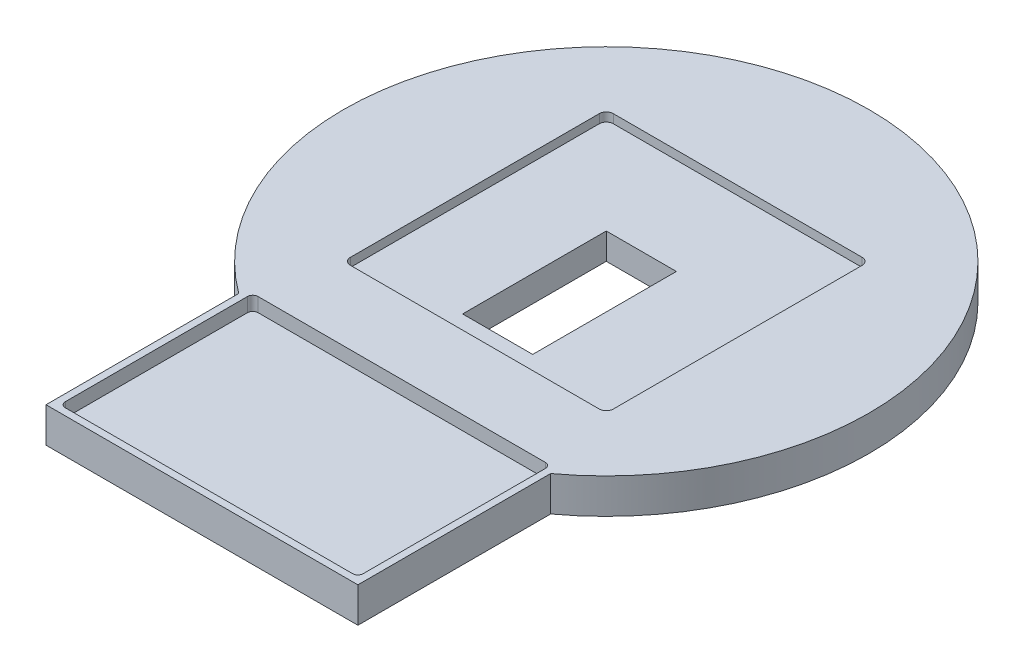
SolidWorks part; units mm, degrees
ref_plane "Front Plane" through (0, 0, 0) normal (0, 0, 1) x (1, 0, 0)
ref_plane "Top Plane" through (0, 0, 0) normal (0, 1, 0) x (1, 0, 0)
ref_plane "Right Plane" through (0, 0, 0) normal (1, 0, 0) x (0, 0, -1)
sketch "Sketch2" plane through (0, 0, 0) normal (0, 1, 0) x (1, 0, 0)
  line L0 (0, 0) -> (-44.5, 0) construction
  line L1 (-44.5, 0) -> (-44.5, -60.3718) construction
  line L2 (-44.5, -60.3718) -> (-44.5, -115.3718)
  line L3 (-44.5, -60.3718) -> (44.5, -60.3718) construction
  line L4 (-44.5, -115.3718) -> (44.5, -115.3718)
  line L5 (44.5, -115.3718) -> (44.5, -60.3718)
  arc A0 (44.5, -60.3718) -> (-44.5, -60.3718) centre (0, 0) ccw
  dimension "D1" = 150
  dimension "D2" = 44.5
  dimension "D3" = 55
extrude "Boss-Extrude2" add sketch "Sketch2" along normal blind 10
sketch "Sketch3" plane through (0, 0, 0) normal (0, 1, 0) x (1, 0, 0)
  line L0 (0, 0) -> (37.5, 0) construction
  line L1 (0, 0) -> (0, 37.5) construction
  line L2 (-37.5, 37.5) -> (37.5, 37.5)
  line L3 (37.5, 37.5) -> (37.5, -37.5)
  line L4 (-37.5, 37.5) -> (-37.5, -37.5)
  line L5 (-37.5, -37.5) -> (37.5, -37.5)
  point P6 (0, 0)
  point P9 (-37.5, 0)
  dimension "D1" = 37.5
extrude "Cut-Extrude2" cut sketch "Sketch3" against normal blind 2.5 from offset 10
fillet "Fillet2" radius 2 4 edges at (37.5, 8.75, 37.5) (-37.5, 8.75, 37.5) (-37.5, 8.75, -37.5) (37.5, 8.75, -37.5)
sketch "Sketch5" plane through (0, 0, 0) normal (0, 1, 0) x (1, 0, 0)
  line L0 (-44.5, -113.3718) -> (-42.5, -113.3718) construction
  line L1 (-44.5, -60.3718) -> (-44.5, -115.3718) construction
  line L2 (-42.5, -113.3718) -> (-42.5, -115.3718) construction
  line L3 (-44.5, -115.3718) -> (44.5, -115.3718) construction
  line L4 (-42.5, -113.3718) -> (-42.5, -58.3718)
  line L5 (-42.5, -58.3718) -> (42.5, -58.3718)
  line L6 (42.5, -58.3718) -> (42.5, -113.3718)
  line L7 (42.5, -113.3718) -> (-42.5, -113.3718)
  dimension "D1" = 2
  dimension "D2" = 85
  dimension "D3" = 55
extrude "Cut-Extrude3" cut sketch "Sketch5" against normal blind 4 from offset 10
fillet "Fillet3" radius 1.5 4 edges at (-42.5, 8, 113.3718) (42.5, 8, 113.3718) (42.5, 8, 58.3718) (-42.5, 8, 58.3718)
sketch "Sketch6" plane through (0, 0, 0) normal (0, 1, 0) x (1, 0, 0)
  line L0 (0, 0) -> (0, 10) construction
  line L1 (-10, 10) -> (10, 10)
  line L2 (10, 10) -> (10, -31)
  line L3 (-10, 10) -> (-10, -31)
  line L4 (-10, -31) -> (10, -31)
  dimension "D1" = 10
  dimension "D2" = 10
  dimension "D3" = 41
extrude "Cut-Extrude4" cut sketch "Sketch6" against normal blind 45 from offset 7.5
